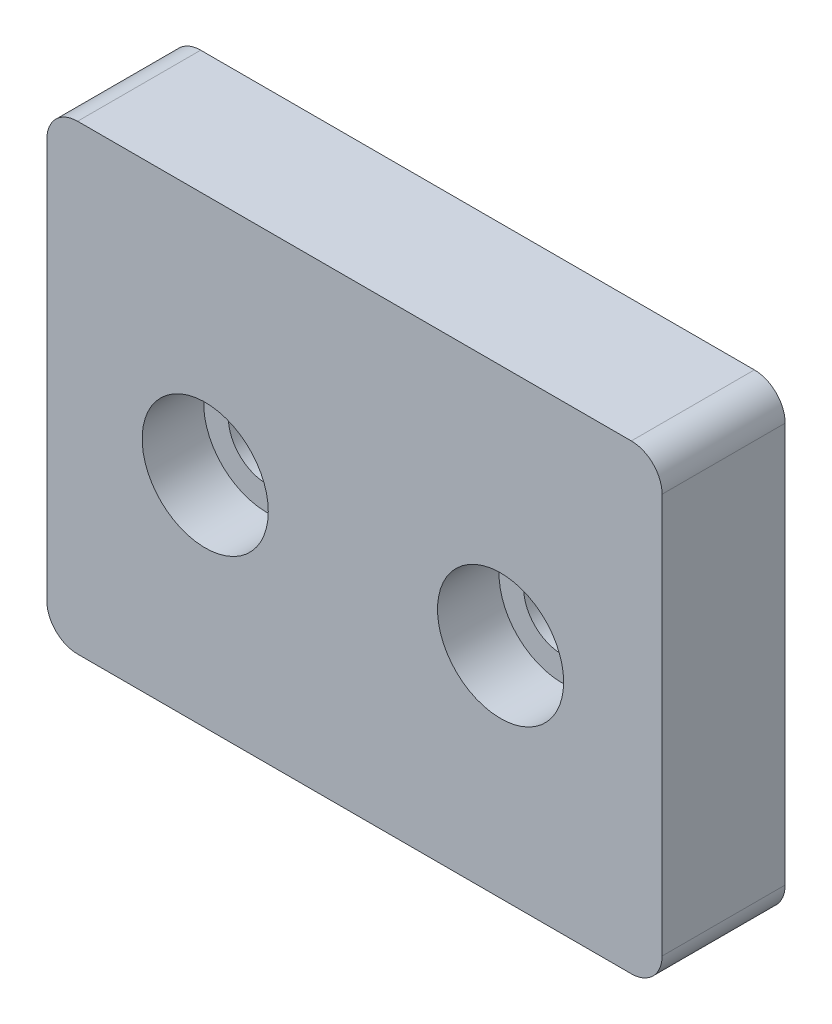
SolidWorks part; units mm, degrees
ref_plane "Front Plane" through (0, 0, 0) normal (0, 0, 1) x (1, 0, 0)
ref_plane "Top Plane" through (0, 0, 0) normal (0, 1, 0) x (1, 0, 0)
ref_plane "Right Plane" through (0, 0, 0) normal (1, 0, 0) x (0, 0, -1)
sketch "Sketch1" plane through (0, 0, 0) normal (0, 0, 1) x (1, 0, 0)
  line L0 (9.9987, 6.6456) -> (-9.9987, 6.6456)
  line L1 (9.9987, 6.6456) -> (9.9987, -8.3544)
  line L2 (9.9987, -8.3544) -> (-9.9987, -8.3544)
  line L3 (-9.9987, 6.6456) -> (-9.9987, -8.3544)
  circle A1 centre (-4.8513, -1.2423) radius 1.25
  circle A2 centre (4.7487, -1.2423) radius 1.25
  dimension "D2" = 2.5
  dimension "D1" = 15
extrude "Boss-Extrude1" add sketch "Sketch1" along normal blind 4
sketch "Sketch2" plane through (0, 0, 4) normal (0, 0, 1) x (1, 0, 0)
  circle A0 centre (-4.8513, -1.2423) radius 2.05
  circle A1 centre (4.7487, -1.2423) radius 2.05
  dimension "D1" = 4.1
extrude "Cut-Extrude1" cut sketch "Sketch2" against normal blind 2
fillet "Fillet1" radius 1 4 edges at (-9.9987, -8.3544, 2) (-9.9987, 6.6456, 2) (9.9987, 6.6456, 2) (9.9987, -8.3544, 2)
